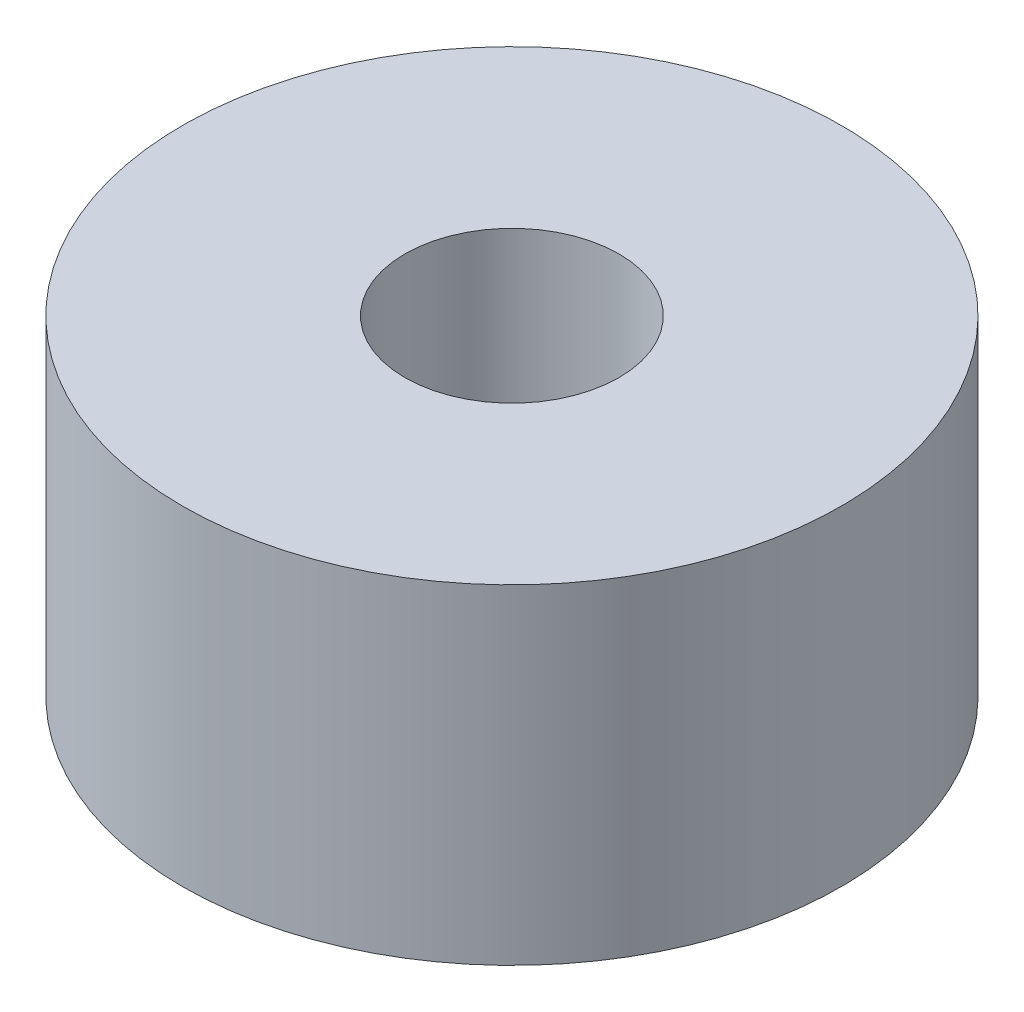
SolidWorks part; units mm, degrees
ref_plane "Plano frontal" through (0, 0, 0) normal (0, 0, 1) x (1, 0, 0)
ref_plane "Plano superior" through (0, 0, 0) normal (0, 1, 0) x (1, 0, 0)
ref_plane "Plano direito" through (0, 0, 0) normal (1, 0, 0) x (0, 0, -1)
sketch "Esboço1" plane through (0, 0, 0) normal (0, 1, 0) x (1, 0, 0)
  circle A0 centre (0, 0) radius 3.25
  circle A1 centre (0, 0) radius 10
  dimension "D1" = 6.5
  dimension "D2" = 20
extrude "Ressalto-extrusão1" add sketch "Esboço1" along normal blind 10
